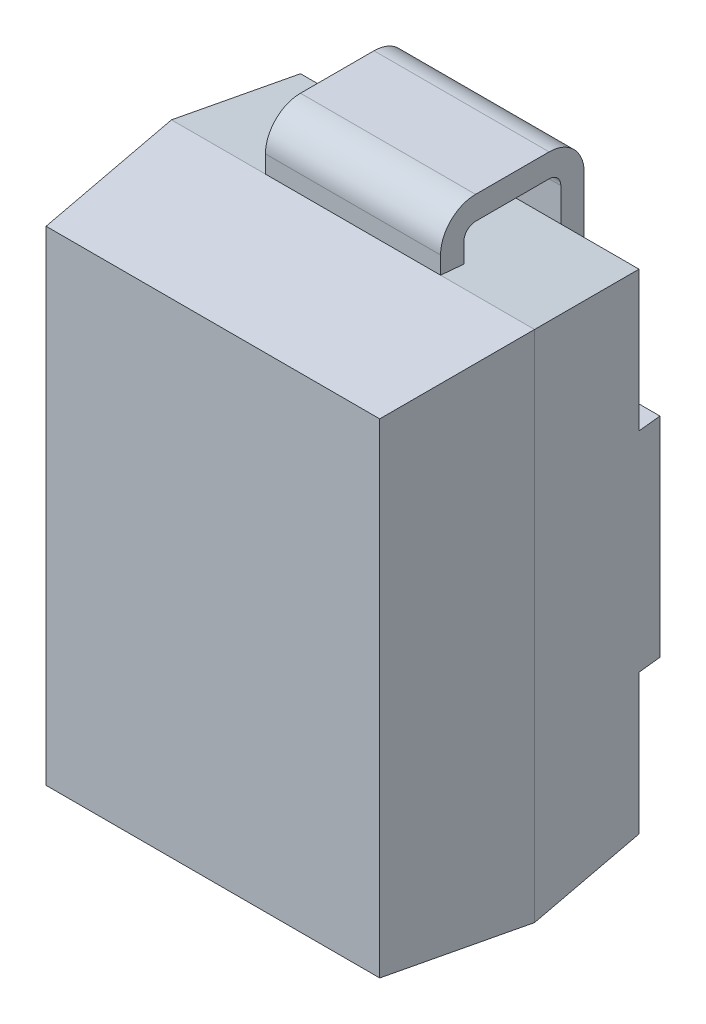
SolidWorks part; units mm, degrees
ref_plane "Front Plane" through (0, 0, 0) normal (0, 0, 1) x (1, 0, 0)
ref_plane "Top Plane" through (0, 0, 0) normal (0, 1, 0) x (1, 0, 0)
ref_plane "Right Plane" through (0, 0, 0) normal (1, 0, 0) x (0, 0, -1)
sketch "Szkic1" plane through (0, 0, 0) normal (0, 0, 1) x (1, 0, 0)
  line L1 (-1.555, -2.2) -> (1.555, -2.2)
  line L2 (-1.555, -2.2) -> (-1.555, 2.2)
  line L3 (-1.555, 2.2) -> (1.555, 2.2)
  line L4 (1.555, -2.2) -> (1.555, 2.2)
  line L5 (-1.555, -2.2) -> (1.555, 2.2) construction
  line L6 (-1.555, 2.2) -> (1.555, -2.2) construction
  point P0 (0, 0)
  dimension "D1" = 4.4
  dimension "D2" = 3.11
extrude "Dodanie-wyciągnięcie1" add sketch "Szkic1" along normal blind 1.2 draft 6
mirror "Lustro1" about plane through (0, 0, 0) normal (0, 0, -1) of bodies 101
sketch "Szkic3" plane through (0, 0, 0) normal (1, 0, 0) x (0, 0, -1)
  line L0 (1.2, -0.895) -> (1.2, 0.895) construction
  line L1 (1.2, -2.0739) -> (1.2, 2.0739) construction
  line L2 (0, 0) -> (1.2, 0) construction
  line L3 (1.2, -0.895) -> (1, -0.895)
  line L4 (1, -0.895) -> (1, 0.895) construction
  line L5 (1, 0.895) -> (1.2, 0.895)
  line L6 (1, -0.895) -> (1, -2.5649)
  line L7 (1, -2.5649) -> (1.2806, -2.5649)
  line L8 (1.2806, -2.5649) -> (1.2, -0.895)
  line L9 (1, 0.895) -> (1, 2.6603)
  line L10 (1, 2.6603) -> (1.4944, 2.6004)
  line L11 (1.4944, 2.6004) -> (1.2, 0.895)
  dimension "D1" = 1.79
  dimension "D2" = 0.2
extrude "Wytnij-wyciągnięcie1" cut sketch "Szkic3" against normal through all and the other way through all
sketch "Szkic5" plane through (0, 0, 0) normal (1, 0, 0) x (0, 0, -1)
  line L0 (0.2, -2.35) -> (0.2, -2.1825)
  line L1 (0.2, -2.1825) -> (0, -2.2)
  line L2 (0, -2.2) -> (0, -2.35)
  line L3 (0.3, -2.65) -> (0.93, -2.65)
  line L4 (1.23, -2.35) -> (1.23, -1.15)
  line L5 (1.23, -1.15) -> (1.03, -1.15)
  line L6 (1.03, -1.15) -> (1.03, -2.35)
  line L7 (0.93, -2.45) -> (0.3, -2.45)
  line L8 (0.93, 2.65) -> (0.3, 2.65)
  line L9 (0, 2.35) -> (0, 2.2)
  line L10 (0, 2.2) -> (0.2, 2.1825)
  line L11 (0.2, 2.1825) -> (0.2, 2.35)
  line L12 (0.3, 2.45) -> (0.93, 2.45)
  line L13 (1.03, 2.35) -> (1.03, 1.15)
  line L14 (1.03, 1.15) -> (1.23, 1.15)
  line L15 (1.23, 1.15) -> (1.23, 2.35)
  line L16 (0, -2.2) -> (0, 2.2) construction
  line L17 (0, 0) -> (-2.0438, 0) construction
  arc A0 (0, -2.35) -> (0.3, -2.65) centre (0.3, -2.35) ccw
  arc A1 (0.93, -2.65) -> (1.23, -2.35) centre (0.93, -2.35) ccw
  arc A2 (0.93, -2.45) -> (1.03, -2.35) centre (0.93, -2.35) ccw
  arc A3 (0.2, -2.35) -> (0.3, -2.45) centre (0.3, -2.35) ccw
  arc A4 (1.23, 2.35) -> (0.93, 2.65) centre (0.93, 2.35) ccw
  arc A5 (0.3, 2.65) -> (0, 2.35) centre (0.3, 2.35) ccw
  arc A6 (0.3, 2.45) -> (0.2, 2.35) centre (0.3, 2.35) ccw
  arc A7 (1.03, 2.35) -> (0.93, 2.45) centre (0.93, 2.35) ccw
extrude "Dodanie-wyciągnięcie2" add sketch "Szkic5" along normal mid plane 1.5 separate body
